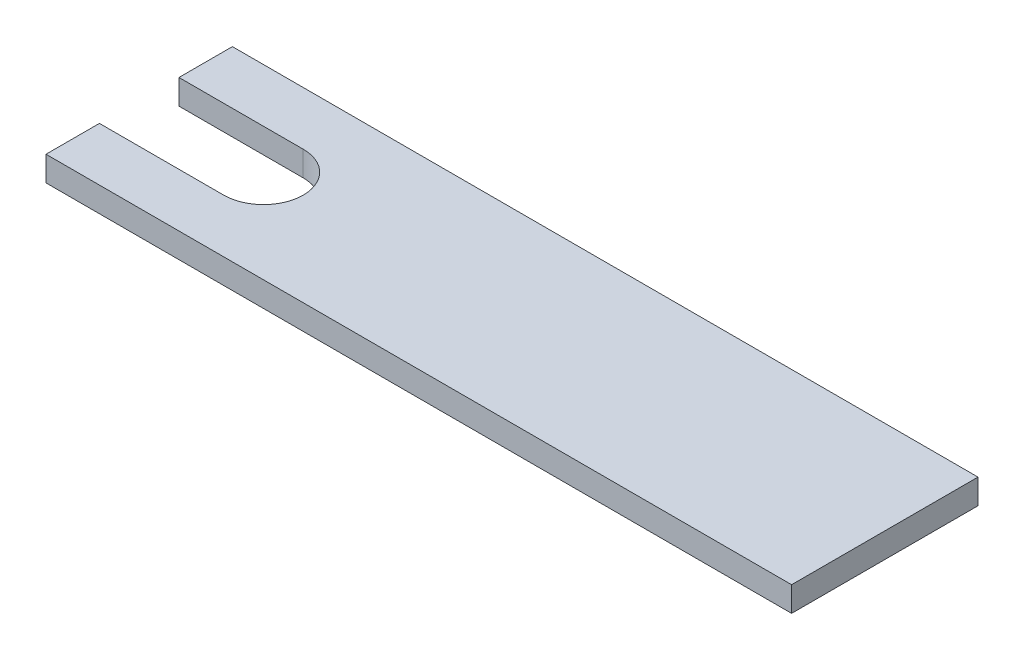
SolidWorks part; units mm, degrees
ref_plane "Front Plane" through (0, 0, 0) normal (0, 0, 1) x (1, 0, 0)
ref_plane "Top Plane" through (0, 0, 0) normal (0, 1, 0) x (1, 0, 0)
ref_plane "Right Plane" through (0, 0, 0) normal (1, 0, 0) x (0, 0, -1)
sketch "Sketch1" plane through (0, 0, 0) normal (0, 1, 0) x (1, 0, 0)
  line L0 (0, 0) -> (5, 0) construction
  line L1 (0, 1.6) -> (5, 1.6)
  line L2 (0, -1.6) -> (5, -1.6)
  line L3 (30, -3.75) -> (0, -3.75)
  line L4 (30, -3.75) -> (30, 3.75)
  line L5 (0, -3.75) -> (0, 3.75)
  line L6 (30, 3.75) -> (0, 3.75)
  line L7 (0, 0) -> (30, 0) construction
  line L8 (15, -3.75) -> (15, 3.75) construction
  arc A0 (0, 1.6) -> (0, -1.6) centre (0, 0) ccw
  arc A1 (5, -1.6) -> (5, 1.6) centre (5, 0) ccw
  point P2 (2.5, 0)
  point P9 (15, 0)
  dimension "D1" = 1.6
  dimension "D2" = 30
  dimension "D3" = 7.5
  dimension "D4" = 5
extrude "Boss-Extrude1" add sketch "Sketch1" along normal blind 1 contours A1 L2 L5 L3 L4 L6 L1
